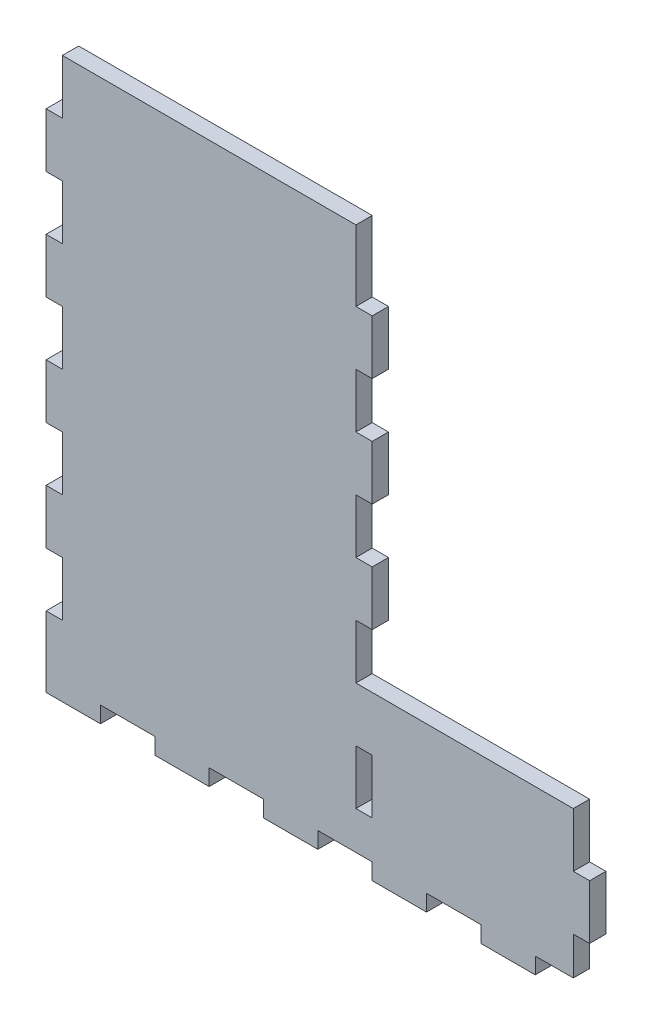
SolidWorks part; units mm, degrees
ref_plane "Front Plane" through (0, 0, 0) normal (0, 0, 1) x (1, 0, 0)
ref_plane "Top Plane" through (0, 0, 0) normal (0, 1, 0) x (1, 0, 0)
ref_plane "Right Plane" through (0, 0, 0) normal (1, 0, 0) x (0, 0, -1)
sketch "Sketch1" plane through (0, 0, 0) normal (0, 0, 1) x (1, 0, 0)
  line L1 (-17.3309, 199.4274) -> (102.6691, 199.4274)
  line L2 (-17.3309, 199.4274) -> (-17.3309, -6.5726)
  line L3 (-17.3309, -6.5726) -> (102.6691, -6.5726)
  line L4 (102.6691, 199.4274) -> (102.6691, 53.4274)
  line L5 (102.6691, -6.5726) -> (182.6691, -6.5726)
  line L7 (102.6691, 53.4274) -> (182.6691, 53.4274)
  line L8 (182.6691, -6.5726) -> (182.6691, 53.4274)
  dimension "D1" = 120
  dimension "D2" = 206
  dimension "D3" = 60
  dimension "D4" = 120
  dimension "D5" = 200
extrude "Boss-Extrude1" add sketch "Sketch1" along normal blind 6
sketch "Sketch2" plane through (0, 0, 6) normal (0, 0, 1) x (1, 0, 0)
  line L0 (-17.3309, -6.5726) -> (182.6691, -6.5726) construction
  line L1 (2.6691, -6.5726) -> (22.6691, -6.5726)
  line L2 (2.6691, -6.5726) -> (2.6691, -0.5726)
  line L3 (2.6691, -0.5726) -> (22.6691, -0.5726)
  line L4 (22.6691, -6.5726) -> (22.6691, -0.5726)
  line L5 (-17.3309, 199.4274) -> (-17.3309, -6.5726) construction
  dimension "D1" = 0
  dimension "D2" = 6
  dimension "D3" = 20
  dimension "D4" = 20
extrude "Cut-Extrude1" cut sketch "Sketch2" against normal through all
pattern_linear "LPattern1" count 5 spacing 40 along (1, 0, 0) of "Cut-Extrude1"
sketch "Sketch3" plane through (0, 0, 0) normal (0, 0, 1) x (1, 0, 0)
  line L5 (102.6691, 53.4274) -> (102.6691, 199.4274) construction
  line L6 (102.6691, 33.4274) -> (96.6691, 33.4274)
  line L7 (102.6691, 33.4274) -> (102.6691, 13.4274)
  line L8 (102.6691, 13.4274) -> (96.6691, 13.4274)
  line L9 (96.6691, 33.4274) -> (96.6691, 13.4274)
  line L10 (62.6691, -6.5726) -> (82.6691, -6.5726) construction
  dimension "D1" = 0
  dimension "D2" = 20
  dimension "D3" = 20
  dimension "D4" = 6
extrude "Cut-Extrude2" cut sketch "Sketch3" along normal through all
pattern_linear "LPattern2" count 5 spacing 40 along (0, 1, 0) of "Cut-Extrude2"
sketch "Sketch4" plane through (0, 0, 6) normal (0, 0, 1) x (1, 0, 0)
  line L1 (96.6691, 193.4274) -> (102.6691, 193.4274)
  line L2 (96.6691, 193.4274) -> (96.6691, 199.4274)
  line L3 (96.6691, 199.4274) -> (102.6691, 199.4274)
  line L4 (102.6691, 193.4274) -> (102.6691, 199.4274)
extrude "Cut-Extrude3" cut sketch "Sketch4" against normal blind 10
sketch "Sketch5" plane through (0, 0, 6) normal (0, 0, 1) x (1, 0, 0)
  line L1 (182.6691, 53.4274) -> (176.6691, 53.4274)
  line L2 (182.6691, 53.4274) -> (182.6691, 33.4274)
  line L3 (182.6691, 33.4274) -> (176.6691, 33.4274)
  line L4 (176.6691, 53.4274) -> (176.6691, 33.4274)
  dimension "D1" = 20
  dimension "D2" = 6
extrude "Cut-Extrude4" cut sketch "Sketch5" against normal blind 10
pattern_linear "LPattern3" count 2 spacing 40 along (0, -1, 0) of "Cut-Extrude4"
sketch "Sketch7" plane through (0, 0, 6) normal (0, 0, 1) x (1, 0, 0)
  line L1 (-17.3309, 199.4274) -> (-11.3309, 199.4274)
  line L2 (-17.3309, 199.4274) -> (-17.3309, 179.4274)
  line L3 (-17.3309, 179.4274) -> (-11.3309, 179.4274)
  line L4 (-11.3309, 199.4274) -> (-11.3309, 179.4274)
  dimension "D1" = 6
  dimension "D2" = 20
extrude "Cut-Extrude5" cut sketch "Sketch7" against normal blind 10
pattern_linear "LPattern4" count 5 spacing 40 along (0, -1, 0) of "Cut-Extrude5"
